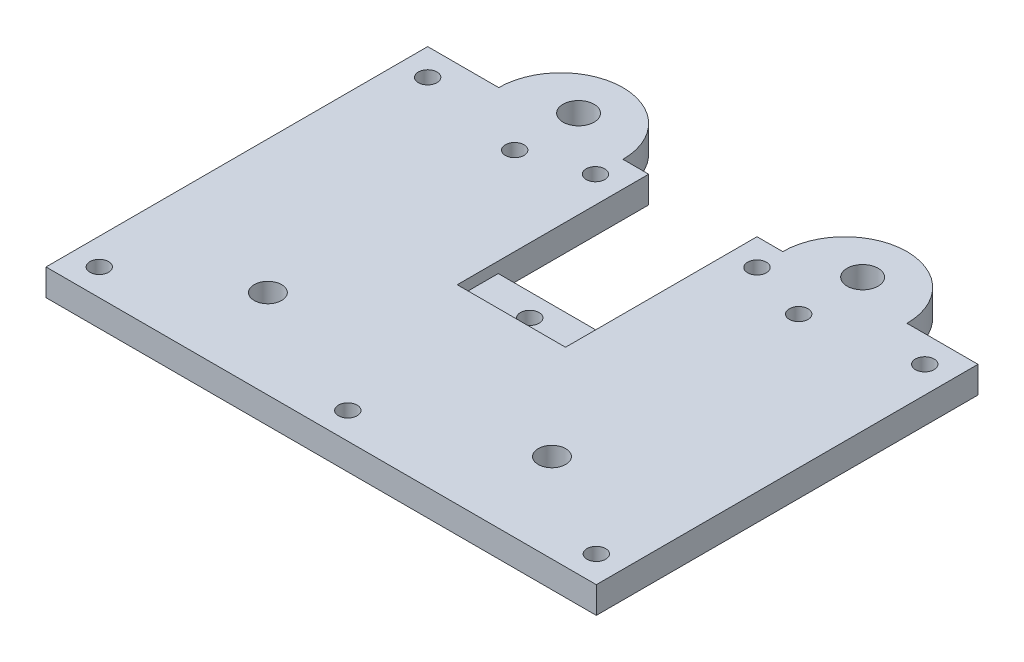
SolidWorks part; units mm, degrees
ref_plane "前视基准面" through (0, 0, 0) normal (0, 0, 1) x (1, 0, 0)
ref_plane "上视基准面" through (0, 0, 0) normal (0, 1, 0) x (1, 0, 0)
ref_plane "右视基准面" through (0, 0, 0) normal (1, 0, 0) x (0, 0, -1)
other "Configuration Table"
sketch "草图1" plane through (0, 0, 0) normal (0, 1, 0) x (1, 0, 0)
  line L0 (31, 43) -> (31, 0) construction
  line L1 (0, 0) -> (62, 0)
  line L2 (0, 0) -> (0, 43)
  line L3 (0, 43) -> (62, 43)
  line L4 (62, 0) -> (62, 43)
  line L5 (0, 21.5) -> (62, 21.5) construction
  line L6 (15, 10) -> (15, 37.8) construction
  circle A0 centre (15, 10) radius 1.55
  circle A1 centre (47, 10) radius 1.55
  circle A2 centre (3, 40) radius 1.05
  circle A3 centre (3, 3) radius 1.05
  circle A4 centre (59, 3) radius 1.05
  circle A5 centre (59, 40) radius 1.05
  circle A6 centre (15, 37.8) radius 1.05
  circle A7 centre (15, 10) radius 1.55
  circle A8 centre (47, 10) radius 1.55
  circle A9 centre (47, 37.8) radius 1.05
  circle A10 centre (31, 3) radius 1.05
  circle A11 centre (31, 23.5) radius 1.05
  circle A12 centre (21.9, 40) radius 1.05
  arc A13 (22, 43) -> (8, 43) centre (15, 43) ccw
  circle A14 centre (40.1, 40) radius 1.05
  circle A15 centre (15, 45) radius 1.75
  circle A16 centre (47, 45) radius 1.75
  arc A17 (40, 43) -> (54, 43) centre (47, 43) cw
  point P40 (0, 0)
  point P41 (0, 0)
  dimension "D3" = 3.1
  dimension "D7" = 2.1
  dimension "D11" = 2.1
  dimension "D12" = 2.1
  dimension "D14" = 2.1
  dimension "D16" = 2.1
  dimension "D19" = 7
  dimension "D21" = 3.5
  dimension "D1" = 62
  dimension "D2" = 43
  dimension "D4" = 15
  dimension "D5" = 27.8
  dimension "D6" = 32
  dimension "D8" = 3
  dimension "D9" = 3
  dimension "D10" = 10
  dimension "D13" = 3
  dimension "D15" = 2
  dimension "D17" = 3
  dimension "D18" = 9.1
  dimension "D20" = 2
extrude "凸台-拉伸1" add sketch "草图1" along normal blind 3 contours L1 L4 L3 L2 A5 A4 A1 A0 A2 A3 A6 A9 | L3 A13 A15 | A17 L3 A16
sketch "草图2" plane through (0, 3, 0) normal (0, 1, 0) x (1, 0, 0)
  line L0 (31, 43) -> (37.1, 43)
  line L1 (0, 43) -> (8, 43) construction
  line L2 (31, 43) -> (24.9, 43)
  line L3 (24.9, 43) -> (24.9, 26.05)
  line L4 (24.9, 26.05) -> (37.1, 26.05)
  line L5 (37.1, 26.05) -> (37.1, 43)
  line L6 (22, 43) -> (40, 43) construction
  circle A0 centre (31, 23.5) radius 1.05 construction
  point P9 (0, 0)
  dimension "D1" = 12.2
  dimension "D2" = 6.1
  dimension "D3" = 2.55
extrude "切除-拉伸1" cut sketch "草图2" against normal blind 10
sketch "草图5" plane through (0, 3, 0) normal (0, 1, 0) x (1, 0, 0)
  line L0 (24.9, 26.05) -> (24.9, 21.43)
  line L1 (24.9, 21.43) -> (37.1, 21.43)
  line L2 (37.1, 26.05) -> (37.1, 21.43)
  line L3 (24.9, 26.05) -> (37.1, 26.05)
  dimension "D1" = 4.62
extrude "切除-拉伸3" cut sketch "草图5" against normal blind 1.22 and the other way through all
